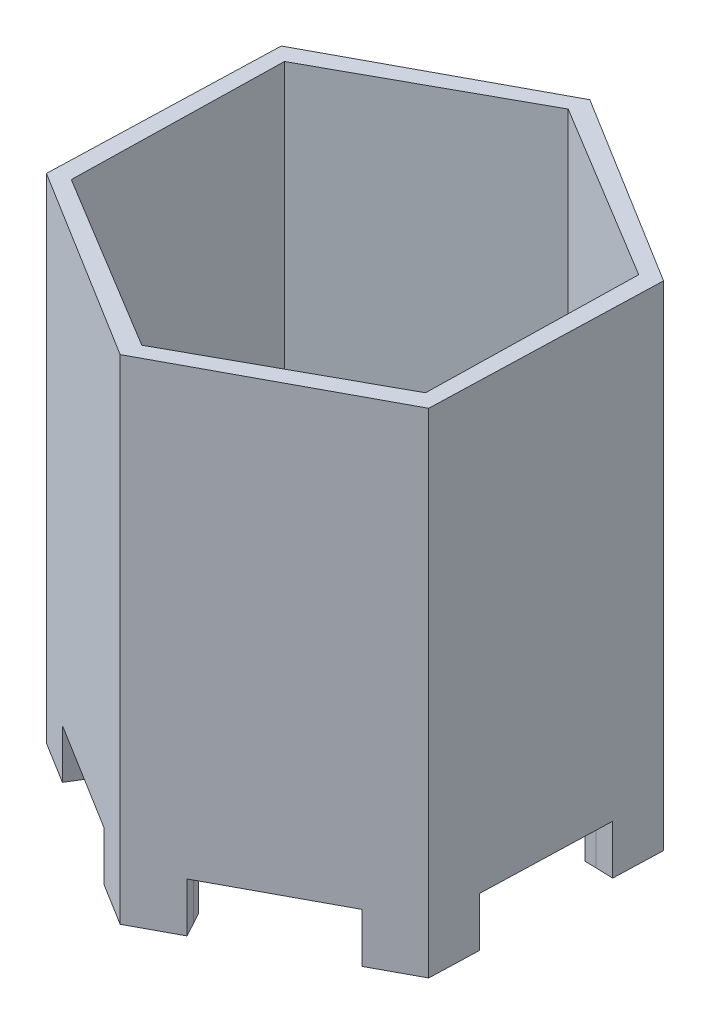
SolidWorks part; units mm, degrees
ref_plane "Front Plane" through (0, 0, 0) normal (0, 0, 1) x (1, 0, 0)
ref_plane "Top Plane" through (0, 0, 0) normal (0, 1, 0) x (1, 0, 0)
ref_plane "Right Plane" through (0, 0, 0) normal (1, 0, 0) x (0, 0, -1)
sketch "Sketch3" plane through (0, 0, 0) normal (0, 1, 0) x (1, 0, 0)
  line L1 (-26.2468, 20.0647) -> (-24.1003, 89.3135)
  line L2 (-24.1003, 89.3135) -> (-82.9982, 125.7968)
  line L3 (-82.9982, 125.7968) -> (-144.0427, 93.0313)
  line L4 (-144.0427, 93.0313) -> (-146.1892, 23.7826)
  line L5 (-146.1892, 23.7826) -> (-87.2913, -12.7008)
  line L6 (-87.2913, -12.7008) -> (-26.2468, 20.0647)
  line L7 (-30.8155, 23.6594) -> (-29.4978, 87.1543)
  line L8 (-29.4978, 87.1543) -> (-83.8271, 120.0429)
  line L9 (-83.8271, 120.0429) -> (-139.4741, 89.4366)
  line L10 (-139.4741, 89.4366) -> (-140.7918, 25.9417)
  line L11 (-140.7918, 25.9417) -> (-86.4625, -6.9468)
  line L12 (-86.4625, -6.9468) -> (-30.8155, 23.6594)
  circle A0 centre (-85.1448, 56.548) radius 60 construction
  circle A1 centre (-85.1448, 56.548) radius 55 construction
  dimension "D1" = 5.8133
extrude "body" add sketch "Sketch3" along normal blind 150
ref_plane "bot plane plane" through (0, 20, 0) normal (0, 1, 0) x (1, 0, 0)
sketch "Sketch7" plane through (0, 20, 0) normal (0, 1, 0) x (1, 0, 0)
  line L1 (-30.8155, 23.6594) -> (-29.4978, 87.1543)
  line L2 (-29.4978, 87.1543) -> (-83.8271, 120.0429)
  line L3 (-83.8271, 120.0429) -> (-139.4741, 89.4366)
  line L4 (-139.4741, 89.4366) -> (-140.7918, 25.9417)
  line L5 (-140.7918, 25.9417) -> (-86.4625, -6.9468)
  line L6 (-86.4625, -6.9468) -> (-30.8155, 23.6594)
  circle A0 centre (-85.1448, 56.548) radius 55 construction
  dimension "D1" = 0
extrude "bot plate" add sketch "Sketch7" along normal blind 10
ref_plane "Body plane 1" through (33.2995, 0, -53.7581) normal (0.5266, 0, -0.8501) x (-0.8501, 0, -0.5266)
sketch "Sketch8" plane through (33.2995, 0, -53.7581) normal (0.5266, 0, -0.8501) x (-0.8501, 0, -0.5266)
  line L0 (67.1489, 0) -> (-67.1489, 0) construction
  line L1 (82.5198, 15) -> (121.8019, 15)
  line L2 (82.5198, 15) -> (82.5198, 0)
  line L3 (82.5198, 0) -> (121.8019, 0)
  line L4 (121.8019, 15) -> (121.8019, 0)
  line L5 (67.5198, 150) -> (67.5198, 0) construction
  line L6 (136.8019, 150) -> (136.8019, 0) construction
  line L7 (67.1489, 20) -> (-67.1489, 20) construction
  dimension "D1" = 15
  dimension "D2" = 15
  dimension "D3" = 5
extrude "leg 1" cut sketch "Sketch8" against normal blind 122.0114
ref_plane "body plane 2" through (-26.843, 0, -0.8321) normal (0.9995, 0, 0.031) x (0.031, 0, -0.9995)
sketch "Sketch9" plane through (-26.843, 0, -0.8321) normal (0.9995, 0, 0.031) x (0.031, 0, -0.9995)
  line L0 (67.1489, 0) -> (-67.1489, 0) construction
  line L1 (34.2419, 15) -> (73.5239, 15)
  line L2 (34.2419, 15) -> (34.2419, 0)
  line L3 (34.2419, 0) -> (73.5239, 0)
  line L4 (73.5239, 15) -> (73.5239, 0)
  line L5 (19.2419, 150) -> (19.2419, 0) construction
  line L6 (88.5239, 150) -> (88.5239, 0) construction
  line L7 (67.1489, 20) -> (-67.1489, 20) construction
  dimension "D1" = 15
  dimension "D2" = 15
  dimension "D3" = 5
extrude "leg 2" cut sketch "Sketch9" against normal blind 125.3372
ref_plane "body plane 3" through (-70.9827, 0, -132.2461) normal (-0.4729, 0, -0.8811) x (-0.8811, 0, 0.4729)
sketch "Sketch10" plane through (-70.9827, 0, -132.2461) normal (-0.4729, 0, -0.8811) x (-0.8811, 0, 0.4729)
  line L0 (13.637, 0) -> (82.919, 0) construction
  line L1 (28.637, 15) -> (67.919, 15)
  line L2 (28.637, 15) -> (28.637, 0)
  line L3 (28.637, 0) -> (67.919, 0)
  line L4 (67.919, 15) -> (67.919, 0)
  line L5 (82.919, 150) -> (82.919, 0) construction
  line L6 (13.637, 150) -> (13.637, 0) construction
  line L7 (67.1489, 20) -> (-67.1489, 20) construction
  dimension "D1" = 15
  dimension "D2" = 15
  dimension "D3" = 5
extrude "leg 3" cut sketch "Sketch10" against normal blind 120.6092
hole_wizard "#9 (0.196) Diameter Hole1" positions "Sketch16" profile "Sketch17" hole size "#9" standard "ANSI Inch" end condition through all
sketch "Sketch16" plane through (0, 30, 0) normal (0, 1, 0) x (1, 0, 0)
  line L0 (-30.8155, 23.6594) -> (-29.4978, 87.1543) construction
  line L1 (-139.4741, 89.4366) -> (-140.7918, 25.9417) construction
  line L2 (-30.8155, 23.6594) -> (-29.4978, 87.1543) construction
  point P0 (-85.1449, 56.5429)
  point P6 (-85.899, 88.3605)
  point P9 (-85.1449, 24.8032)
  point P13 (-112.6547, 56.356)
  point P18 (-57.6353, 56.7182)
  point P23 (-112.6547, 88.3427)
  point P25 (-112.6547, 24.8032)
  point P27 (-57.6353, 24.8032)
  point P29 (-57.6353, 88.3427)
  point P31 (-98.564, 72.6277)
  point P34 (-71.058, 72.6315)
  point P35 (-71.058, 40.6822)
  point P37 (-98.564, 40.6822)
  point P39 (-130.2291, 72.6277)
  point P41 (-130.2291, 40.6822)
  point P43 (-40.1781, 40.6822)
  point P45 (-40.1781, 72.6315)
  point P47 (-85.1449, 8.3563)
  point P49 (-85.6045, 106.0057)
  dimension "D1" = 55
  dimension "D2" = 63.5
  dimension "D3" = 31.75
  dimension "D4" = 31.75
  dimension "D5" = 27.5
  dimension "D6" = 27.5
  dimension "D7" = 41.25
  dimension "D8" = 41.25
sketch "Sketch17" plane through (-85.1449, 30, -56.5429) normal (1, 0, 0) x (0, 0, 1)
  line L0 (0, 0) -> (0, 30)
  line L1 (0, 30) -> (2.4892, 30)
  line L2 (2.4892, 30) -> (2.4892, 0)
  line L5 (2.4892, 0) -> (0, 0)
  line L11 (0, -6.35) -> (0, 107.95) construction
  dimension "Thru Hole Dia." = 4.9784
  dimension "Thru Hole Depth" = 30
sketch "Sketch18" plane through (-70.9827, 0, -132.2461) normal (-0.4729, 0, -0.8811) x (-0.8811, 0, 0.4729)
  line L0 (13.637, 150) -> (82.919, 150) construction
  line L1 (31.137, 150) -> (65.419, 150)
  line L2 (31.137, 150) -> (31.137, 135)
  line L3 (31.137, 135) -> (65.419, 135)
  line L4 (65.419, 150) -> (65.419, 135)
  line L6 (13.637, 150) -> (13.637, 0) construction
  line L7 (82.919, 150) -> (82.919, 0) construction
  dimension "D1" = 17.5
  dimension "D2" = 17.5
ref_plane "sensor stand plane" through (0, 150, 0) normal (0, 1, 0) x (1, 0, 0)
sketch "Sketch23" plane through (-26.843, 0, -0.8321) normal (0.9995, 0, 0.031) x (0.031, 0, -0.9995)
  line L0 (67.1489, 150) -> (-67.1489, 150) construction
  line L1 (88.5239, 150) -> (88.5239, 0) construction
  circle A0 centre (56.0239, 150) radius 10.5
  circle A1 centre (56.0239, 150) radius 15
  dimension "D1" = 0
  dimension "D2" = 32.5
sketch "Sketch24" plane through (-70.9827, 0, -132.2461) normal (-0.4729, 0, -0.8811) x (-0.8811, 0, 0.4729)
  text T0 "WLGYL\r\n  by H"
extrude "Cut-Extrude1" cut sketch "Sketch24" against normal blind 1
sketch "Sketch26" plane through (0, 20, 0) normal (0, -1, 0) x (1, 0, 0)
  line L10 (-97.3057, 0.3828) -> (-86.4625, 6.9468)
  line L11 (-140.7918, -25.9417) -> (-86.4625, 6.9468) construction
  line L12 (-86.4625, 6.9468) -> (-76.343, 1.381)
  line L13 (-76.343, 1.381) -> (-78.1944, -1.9851)
  line L14 (-78.1944, -1.9851) -> (-86.4625, 2.5624)
  line L15 (-86.4625, 2.5624) -> (-95.5085, -2.5861)
  line L16 (-95.5085, -2.5861) -> (-97.3057, 0.3828)
extrude "Boss-Extrude5" add sketch "Sketch26" along normal blind 20
sketch "Sketch30" plane through (0, 20, 0) normal (0, -1, 0) x (1, 0, 0)
  line L10 (-41.8604, -17.5387) -> (-30.7563, -23.6511)
  line L12 (-30.7563, -23.6511) -> (-30.5207, -35.1979)
  line L13 (-30.5207, -35.1979) -> (-34.3616, -35.2762)
  line L14 (-34.3616, -35.2762) -> (-34.5541, -25.842)
  line L15 (-34.5541, -25.842) -> (-43.534, -20.5791)
  line L16 (-43.534, -20.5791) -> (-41.8604, -17.5387)
extrude "Boss-Extrude7" add sketch "Sketch30" along normal blind 20
sketch "Sketch31" plane through (0, 20, 0) normal (0, -1, 0) x (1, 0, 0)
  line L10 (-29.7604, -74.4855) -> (-29.4974, -87.1581)
  line L12 (-29.4974, -87.1581) -> (-39.3773, -93.139)
  line L13 (-39.3773, -93.139) -> (-41.3668, -89.8525)
  line L14 (-41.3668, -89.8525) -> (-33.2945, -84.9659)
  line L15 (-33.2945, -84.9659) -> (-33.2302, -74.5576)
  line L16 (-33.2302, -74.5576) -> (-29.7604, -74.4855)
extrude "Boss-Extrude8" add sketch "Sketch31" along normal blind 20
sketch "Sketch32" plane through (0, 20, 0) normal (0, -1, 0) x (1, 0, 0)
  line L10 (-140.5762, -38.614) -> (-140.8392, -25.9414)
  line L12 (-140.8392, -25.9414) -> (-130.9594, -19.9606)
  line L13 (-130.9594, -19.9606) -> (-128.9699, -23.247)
  line L14 (-128.9699, -23.247) -> (-137.0422, -28.1336)
  line L15 (-137.0422, -28.1336) -> (-137.1065, -38.542)
  line L16 (-137.1065, -38.542) -> (-140.5762, -38.614)
extrude "Boss-Extrude9" add sketch "Sketch32" along normal blind 20
sketch "Sketch36" plane through (0, 20, 0) normal (0, -1, 0) x (1, 0, 0)
  line L10 (-72.9824, -113.5011) -> (-83.8257, -120.0652)
  line L12 (-83.8257, -120.0652) -> (-93.9452, -114.4994)
  line L13 (-93.9452, -114.4994) -> (-92.0938, -111.1332)
  line L14 (-92.0938, -111.1332) -> (-83.8257, -115.6807)
  line L15 (-83.8257, -115.6807) -> (-74.7797, -110.5322)
  line L16 (-74.7797, -110.5322) -> (-72.9824, -113.5011)
extrude "Boss-Extrude10" add sketch "Sketch36" along normal blind 20
sketch "Sketch37" plane through (0, 20, 0) normal (0, -1, 0) x (1, 0, 0)
  line L10 (-128.4292, -95.5626) -> (-139.5333, -89.4502)
  line L12 (-139.5333, -89.4502) -> (-139.7689, -77.9035)
  line L13 (-139.7689, -77.9035) -> (-135.928, -77.8251)
  line L14 (-135.928, -77.8251) -> (-135.7355, -87.2593)
  line L15 (-135.7355, -87.2593) -> (-126.7556, -92.5223)
  line L16 (-126.7556, -92.5223) -> (-128.4292, -95.5626)
extrude "Boss-Extrude11" add sketch "Sketch37" along normal blind 20
